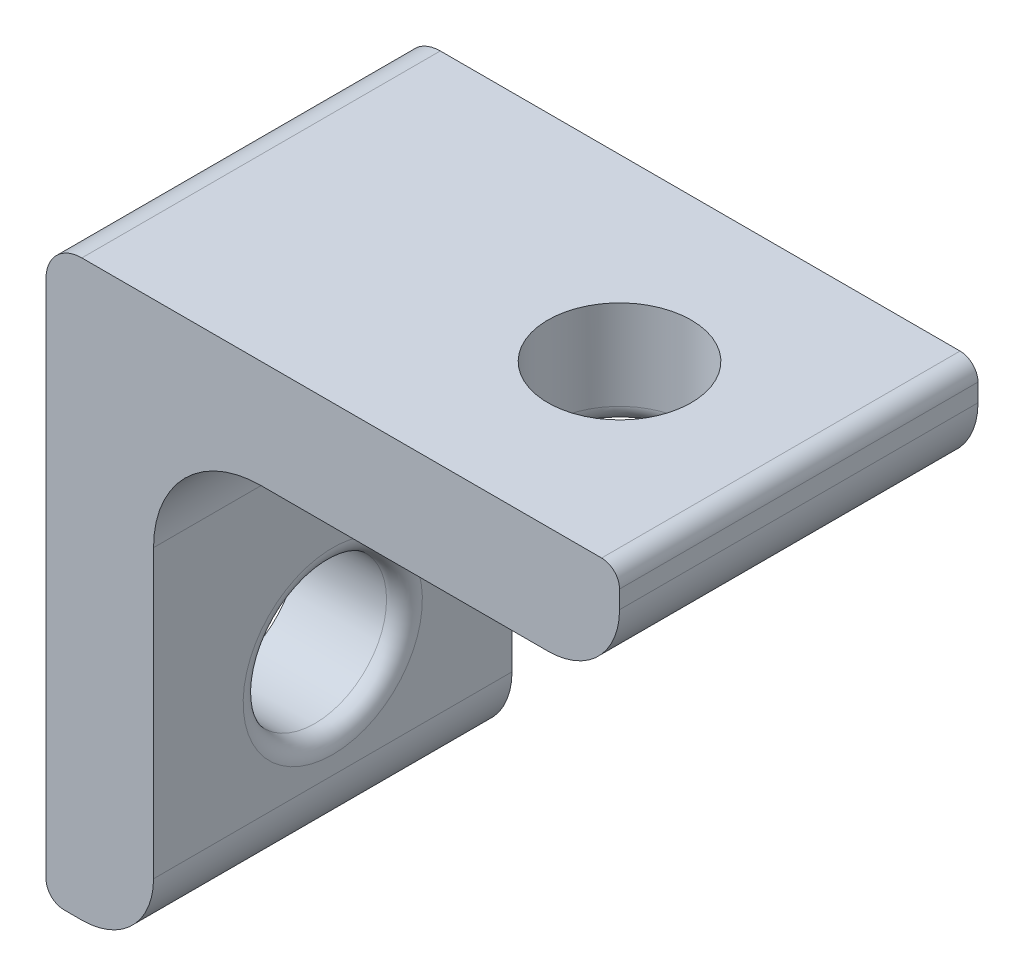
SolidWorks part; units mm, degrees
material "自定义塑料"
ref_plane "前视基准面" through (0, 0, 0) normal (0, 0, 1) x (1, 0, 0)
ref_plane "上视基准面" through (0, 0, 0) normal (0, 1, 0) x (1, 0, 0)
ref_plane "右视基准面" through (0, 0, 0) normal (1, 0, 0) x (0, 0, -1)
sketch "草图1" plane through (0, 0, 0) normal (0, 0, 1) x (1, 0, 0)
  line L1 (-13, 0) -> (-13, -11)
  line L2 (-15, -13) -> (-15.5, -13)
  line L3 (-16, -12.5) -> (-16, 3)
  line L5 (0, -55) -> (0, 55) construction
  line L9 (-16, 3) -> (-0.5, 3)
  line L10 (-13, 0) -> (-2, 0)
  line L14 (0, 2.5) -> (0, 2)
  arc A0 (-16, -12.5) -> (-15.5, -13) centre (-15.5, -12.5) ccw
  arc A1 (-13, -11) -> (-15, -13) centre (-15, -11) cw
  arc A2 (0, 2) -> (-2, 0) centre (-2, 2) cw
  arc A3 (0, 2.5) -> (-0.5, 3) centre (-0.5, 2.5) ccw
  point P11 (0, 0)
  point P15 (0, 0)
  point P17 (-16, -13)
  point P20 (-13, -13)
  point P21 (0, 3)
  point P23 (0, 0)
  point P24 (0, 3)
  dimension "D5" = 0.5
  dimension "D6" = 2
  dimension "D7" = 2
  dimension "D8" = 0.5
  dimension "D1" = 13
  dimension "D2" = 3
  dimension "D3" = 3
  dimension "D4" = 16
extrude "凸台-拉伸1" add sketch "草图1" along normal blind 10
sketch "草图2" plane through (-13, 0, 0) normal (1, 0, 0) x (0, 0, -1)
  line L2 (0, -11) -> (0, 0) construction
  line L3 (-10, 3) -> (0, 3) construction
  circle A0 centre (-5, -8) radius 2
  dimension "D1" = 4
  dimension "D2" = 5
  dimension "D3" = 11
sketch "草图4" plane through (0, 0, 0) normal (0, 1, 0) x (1, 0, 0)
  line L0 (-0.5, 0) -> (-16, 0) construction
  line L1 (0, -10) -> (0, 0) construction
  circle A0 centre (-5, -5) radius 2
  dimension "D1" = 4
  dimension "D2" = 5
  dimension "D3" = 5
extrude "切除-拉伸1" cut sketch "草图4" along normal blind 10
extrude "切除-拉伸2" cut sketch "草图2" against normal blind 20
fillet "圆角2" radius 0.5 2 edges at (-13, -8, 3) (-5, 0, 7)
fillet "圆角3" radius 3 1 edges at (-13, 0, 5)
fillet "圆角4" radius 1 1 edges at (-16, 3, 5)
